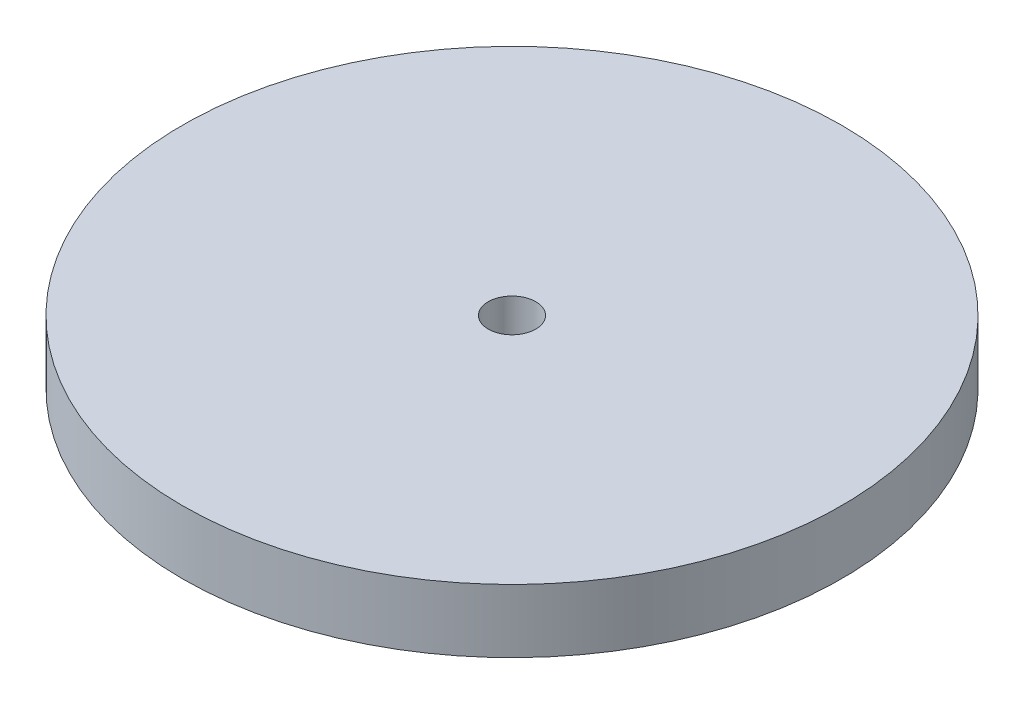
SolidWorks part; units mm, degrees
material "Balsa"
ref_plane "Front Plane" through (0, 0, 0) normal (0, 0, 1) x (1, 0, 0)
ref_plane "Top Plane" through (0, 0, 0) normal (0, 1, 0) x (1, 0, 0)
ref_plane "Right Plane" through (0, 0, 0) normal (1, 0, 0) x (0, 0, -1)
sketch "Sketch1" plane through (0, 0, 0) normal (0, 1, 0) x (1, 0, 0)
  circle A0 centre (0, 0) radius 66.04
  dimension "D1" = 132.08
extrude "Boss-Extrude1" add sketch "Sketch1" along normal blind 12.7
sketch "Sketch2" plane through (0, 12.7, 0) normal (0, 1, 0) x (1, 0, 0)
  circle A0 centre (0, 0) radius 4.7625
  dimension "D1" = 9.525
extrude "Cut-Extrude1" cut sketch "Sketch2" against normal blind 12.7
